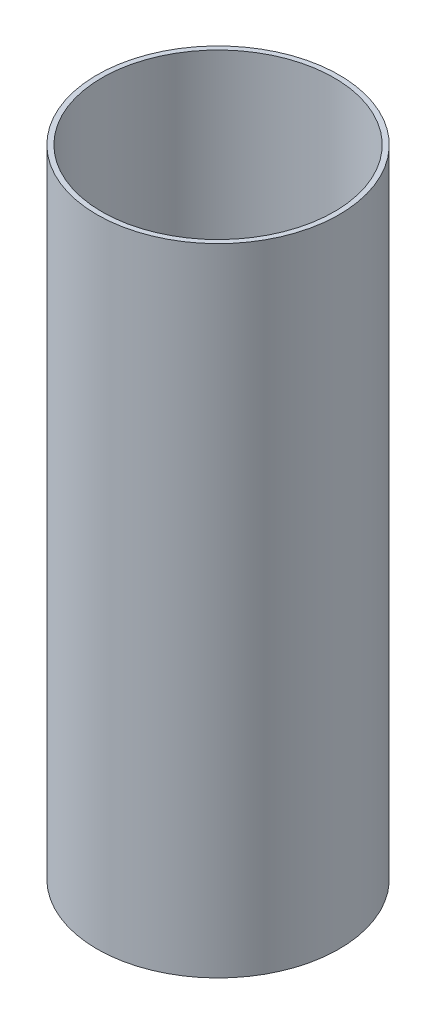
SolidWorks part; units mm, degrees
ref_plane "Front Plane" through (0, 0, 0) normal (0, 0, 1) x (1, 0, 0)
ref_plane "Top Plane" through (0, 0, 0) normal (0, 1, 0) x (1, 0, 0)
ref_plane "Right Plane" through (0, 0, 0) normal (1, 0, 0) x (0, 0, -1)
sketch "Sketch1" plane through (0, 0, 0) normal (0, 1, 0) x (1, 0, 0)
  circle A0 centre (0, 0) radius 38.0746
  circle A1 centre (0, 0) radius 36.5125
  dimension "D1" = 76.1492
  dimension "D2" = 73.025
extrude "Boss-Extrude1" add sketch "Sketch1" along normal blind 200
